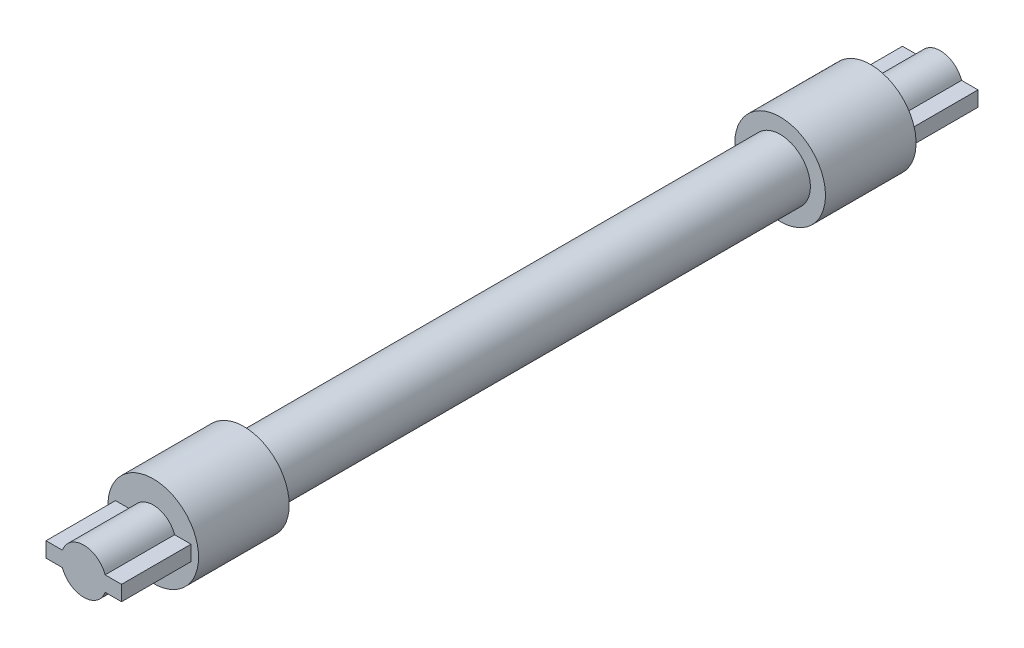
SolidWorks part; units mm, degrees
ref_plane "Front" through (0, 0, 0) normal (0, 0, 1) x (1, 0, 0)
ref_plane "Top" through (0, 0, 0) normal (0, 1, 0) x (1, 0, 0)
ref_plane "Right" through (0, 0, 0) normal (1, 0, 0) x (0, 0, -1)
sketch "Sketch1" plane through (0, 0, 0) normal (0, 0, 1) x (1, 0, 0)
  circle A0 centre (0, 0) radius 40
extrude "Boss-Extrude1" add sketch "Sketch1" along normal blind 710
sketch "Sketch2" plane through (0, 0, 710) normal (0, 0, 1) x (1, 0, 0)
  circle A0 centre (0, 0) radius 60
  dimension "D1" = 120
extrude "Boss-Extrude2" add sketch "Sketch2" along normal blind 120
sketch "Sketch3" plane through (0, 0, 0) normal (0, 0, -1) x (-1, 0, 0)
  circle A0 centre (0, 0) radius 60
  dimension "D1" = 120
extrude "Boss-Extrude3" add sketch "Sketch3" along normal blind 120
sketch "Sketch4" plane through (0, 0, 830) normal (0, 0, 1) x (1, 0, 0)
  line L0 (-50, 10) -> (50, 10)
  line L1 (-50, 10) -> (-50, -10)
  line L2 (-50, -10) -> (50, -10)
  line L3 (50, 10) -> (50, -10)
  circle A0 centre (0, 0) radius 30
  dimension "D5" = 60
  dimension "D1" = 50
  dimension "D2" = 100
  dimension "D3" = 10
  dimension "D4" = 20
extrude "Boss-Extrude4" add sketch "Sketch4" along normal blind 92 contours A0 L0 L1 L2 | L0 A0 | L0 A0 L2 | L2 A0 | A0 L2 L3 L0
sketch "Sketch5" plane through (0, 0, -120) normal (0, 0, -1) x (-1, 0, 0)
  line L0 (50, -10) -> (-50, -10)
  line L1 (50, -10) -> (50, 10)
  line L2 (50, 10) -> (-50, 10)
  line L3 (-50, -10) -> (-50, 10)
  circle A0 centre (0, 0) radius 30
  dimension "D3" = 60
  dimension "D1" = 50
  dimension "D2" = 100
  dimension "D4" = 10
  dimension "D5" = 20
extrude "Boss-Extrude5" add sketch "Sketch5" along normal blind 92 contours L2 A0 | A0 L2 L3 L0 | L2 A0 L0 | L0 A0 | A0 L0 L1 L2
